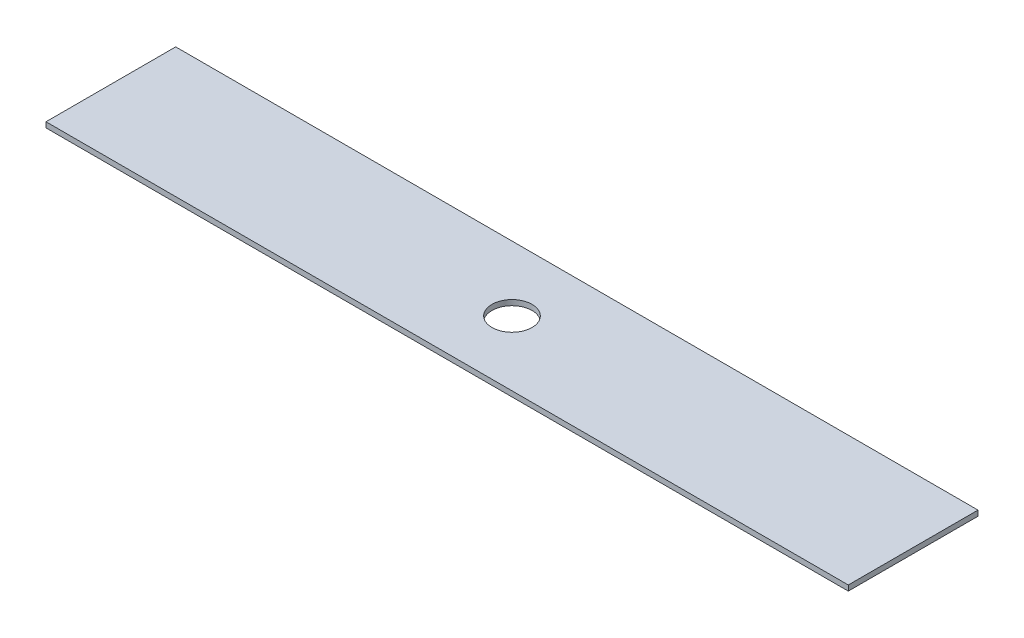
SolidWorks part; units mm, degrees
ref_plane "Front Plane" through (0, 0, 0) normal (0, 0, 1) x (1, 0, 0)
ref_plane "Top Plane" through (0, 0, 0) normal (0, 1, 0) x (1, 0, 0)
ref_plane "Right Plane" through (0, 0, 0) normal (1, 0, 0) x (0, 0, -1)
sketch "Sketch1" plane through (0, 0, 0) normal (0, 1, 0) x (1, 0, 0)
  line L1 (-102.5523, 9.0994) -> (197.4477, 9.0994)
  line L2 (-102.5523, 9.0994) -> (-102.5523, -39.4006)
  line L3 (-102.5523, -39.4006) -> (197.4477, -39.4006)
  line L4 (197.4477, 9.0994) -> (197.4477, -39.4006)
  dimension "D1" = 300
  dimension "D2" = 48.5
extrude "Boss-Extrude1" add sketch "Sketch1" along normal blind 2 contours L2 L3 L4 L1
sketch "Sketch2" plane through (0, 2, 0) normal (0, 1, 0) x (1, 0, 0)
  circle A0 centre (47.4477, -15.1506) radius 7.5
extrude "Cut-Extrude1" cut sketch "Sketch2" against normal blind 2
